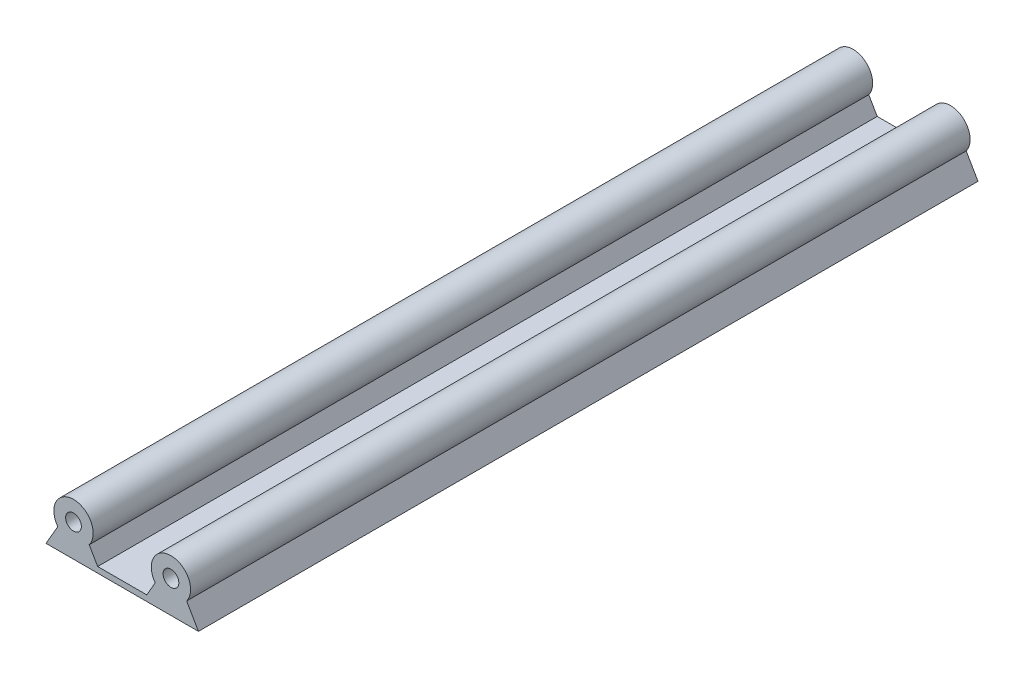
SolidWorks part; units mm, degrees
ref_plane "Front Plane" through (0, 0, 0) normal (0, 0, 1) x (1, 0, 0)
ref_plane "Top Plane" through (0, 0, 0) normal (0, 1, 0) x (1, 0, 0)
ref_plane "Right Plane" through (0, 0, 0) normal (1, 0, 0) x (0, 0, -1)
sketch "Sketch1" plane through (0, 0, 0) normal (0, 0, 1) x (1, 0, 0)
  line L0 (-4, -3) -> (4, -3) construction
  line L1 (-4, -3) -> (-7, -8.1962)
  line L2 (4, -3) -> (7, -8.1962)
  line L3 (-7, -8.1962) -> (7, -8.1962)
  line L4 (28.8, -3) -> (31.8, -8.1962)
  line L5 (17.8, -8.1962) -> (31.8, -8.1962)
  line L6 (20.8, -3) -> (17.8, -8.1962)
  circle A0 centre (0, 0) radius 5
  arc A1 (-4, -3) -> (4, -3) centre (0, 0) cw
  arc A2 (20.8, -3) -> (28.8, -3) centre (24.8, 0) cw
  dimension "D1" = 3
  dimension "D2" = 2
  dimension "D3" = 8
extrude "Boss-Extrude1" add sketch "Sketch1" along normal blind 220 contours A0 L0 | L0 A0 | A0 L1 L3 L2 | L4 L5 L6 A2
sketch "Sketch3" plane through (0, 0, 220) normal (0, 0, 1) x (1, 0, 0)
  line L0 (7, -8.1962) -> (17.8, -8.1962)
  line L1 (6.15, -6.7239) -> (18.65, -6.7239)
  line L2 (4, -3) -> (7, -8.1962) construction
  line L3 (20.8, -3) -> (17.8, -8.1962) construction
  line L4 (18.65, -6.7239) -> (18.65, -8.1962)
  line L5 (17.8, -8.1962) -> (31.8, -8.1962) construction
  line L6 (18.65, -8.1962) -> (17.8, -8.1962)
  line L7 (6.15, -6.7239) -> (6.15, -8.1962)
  line L8 (-7, -8.1962) -> (7, -8.1962) construction
  line L9 (6.15, -8.1962) -> (7, -8.1962)
  dimension "D1" = 12.5
sketch "Sketch4" plane through (0, -8.1962, 0) normal (0, -1, 0) x (1, 0, 0)
  line L0 (24.8, 220) -> (24.8, 0) construction
  line L1 (17.8, 220) -> (31.8, 220) construction
  line L2 (17.8, 0) -> (31.8, 0) construction
  line L3 (0, 0) -> (0, 220) construction
  line L4 (-7, 220) -> (7, 220) construction
  circle A0 centre (0, 198.2) radius 3.2
  circle A1 centre (24.8, 198.2) radius 3.2
  circle A2 centre (24.8, 173.2) radius 3.2
  circle A3 centre (24.8, 148.2) radius 3.2
  circle A4 centre (24.8, 123.2) radius 3.2
  circle A5 centre (24.8, 98.2) radius 3.2
  circle A6 centre (24.8, 73.2) radius 3.2
  circle A7 centre (24.8, 48.2) radius 3.2
  circle A8 centre (24.8, 23.2) radius 3.2
  circle A9 centre (0, 173.2) radius 3.2
  circle A10 centre (0, 148.2) radius 3.2
  circle A11 centre (0, 123.2) radius 3.2
  circle A12 centre (0, 98.2) radius 3.2
  circle A13 centre (0, 73.2) radius 3.2
  circle A14 centre (0, 48.2) radius 3.2
  circle A15 centre (0, 23.2) radius 3.2
  dimension "D1" = 2
  dimension "D4" = 6.4
  dimension "D3" = 23.2
  dimension "D2" = 8
extrude "Boss-Extrude4" add sketch "Sketch3" against normal blind 220
sketch "Sketch5" plane through (0, 0, 0) normal (0, 0, -1) x (-1, 0, 0)
  circle A0 centre (0, 0) radius 1.37
  circle A1 centre (-24.8, 0) radius 1.37
  dimension "D1" = 2
extrude "Cut-Extrude1" cut sketch "Sketch5" against normal blind 7
sketch "Sketch6" plane through (0, 0, 220) normal (0, 0, 1) x (1, 0, 0)
  circle A0 centre (0, 0) radius 1.37
  circle A1 centre (24.8, 0) radius 1.37
  dimension "D1" = 2
extrude "Cut-Extrude2" cut sketch "Sketch6" against normal blind 7
sketch "Sketch9" plane through (0, 0, 0) normal (0, 0, -1) x (-1, 0, 0)
  line L6 (-28.8, -3) -> (-31.8, -8.1962)
  line L7 (-31.8, -8.1962) -> (7, -8.1962)
  line L8 (7, -8.1962) -> (4, -3)
  line L9 (-4, -3) -> (-6.15, -6.7239)
  line L10 (-6.15, -6.7239) -> (-18.65, -6.7239)
  line L11 (-18.65, -6.7239) -> (-20.8, -3)
  line L12 (-28.8, -3) -> (-31.8, -8.1962)
  line L13 (-31.8, -8.1962) -> (7, -8.1962)
  line L14 (7, -8.1962) -> (4, -3)
  line L15 (-4, -3) -> (-6.15, -6.7239)
  line L16 (-6.15, -6.7239) -> (-18.65, -6.7239)
  line L17 (-18.65, -6.7239) -> (-20.8, -3)
  arc A2 (4, -3) -> (-4, -3) centre (0, 0) ccw
  arc A3 (-20.8, -3) -> (-28.8, -3) centre (-24.8, 0) ccw
  arc A4 (4, -3) -> (-4, -3) centre (0, 0) ccw
  arc A5 (-20.8, -3) -> (-28.8, -3) centre (-24.8, 0) ccw
  dimension "D1" = 0
extrude "Cut-Extrude4" cut sketch "Sketch9" against normal blind 10.8
sketch "Sketch10" plane through (0, 0, 220) normal (0, 0, 1) x (1, 0, 0)
  line L6 (20.8, -3) -> (18.65, -6.7239)
  line L7 (18.65, -6.7239) -> (6.15, -6.7239)
  line L8 (6.15, -6.7239) -> (4, -3)
  line L9 (-4, -3) -> (-7, -8.1962)
  line L10 (-7, -8.1962) -> (31.8, -8.1962)
  line L11 (31.8, -8.1962) -> (28.8, -3)
  line L12 (20.8, -3) -> (18.65, -6.7239)
  line L13 (18.65, -6.7239) -> (6.15, -6.7239)
  line L14 (6.15, -6.7239) -> (4, -3)
  line L15 (-4, -3) -> (-7, -8.1962)
  line L16 (-7, -8.1962) -> (31.8, -8.1962)
  line L17 (31.8, -8.1962) -> (28.8, -3)
  arc A2 (4, -3) -> (-4, -3) centre (0, 0) ccw
  arc A3 (28.8, -3) -> (20.8, -3) centre (24.8, 0) ccw
  arc A4 (4, -3) -> (-4, -3) centre (0, 0) ccw
  arc A5 (28.8, -3) -> (20.8, -3) centre (24.8, 0) ccw
  dimension "D1" = 0
extrude "Cut-Extrude5" cut sketch "Sketch10" against normal blind 10.8
sketch "Sketch11" plane through (0, 0, 209.2) normal (0, 0, 1) x (1, 0, 0)
  circle A0 centre (0, 0) radius 2
  circle A1 centre (24.8, 0) radius 2
  dimension "D1" = 2
extrude "Cut-Extrude6" cut sketch "Sketch11" against normal blind 7
sketch "Sketch12" plane through (0, 0, 10.8) normal (0, 0, -1) x (-1, 0, 0)
  circle A0 centre (0, 0) radius 1.5
  circle A1 centre (-24.8, 0) radius 1.5
  dimension "D1" = 2
  dimension "D2" = 3
extrude "Cut-Extrude7" cut sketch "Sketch12" against normal blind 7
sketch "Sketch13" plane through (0, 0, 209.2) normal (0, 0, 1) x (1, 0, 0)
  line L0 (-7, -8.1962) -> (31.8, -8.1962) construction
  line L1 (-12.6, 41.8038) -> (37.4, 41.8038)
  line L2 (-12.6, 41.8038) -> (-12.6, -8.1962)
  line L3 (-12.6, -8.1962) -> (37.4, -8.1962)
  line L4 (37.4, 41.8038) -> (37.4, -8.1962)
  point P8 (12.4, -8.1962)
  point P9 (12.4, -8.1962)
  dimension "D1" = 50
  dimension "D2" = 50
extrude "Boss-Extrude5" [suppressed] add sketch "Sketch13" against normal blind 10
sketch "Sketch14" [suppressed] plane through (0, 0, 199.2) normal (0, 0, -1) x (-1, 0, 0)
  line L0 (-12.4, -8.1962) -> (-12.4, 41.8038) construction
  line L1 (-31.8, -8.1962) -> (7, -8.1962) construction
  line L2 (-37.4, 41.8038) -> (12.6, 41.8038) construction
  circle A0 centre (-12.4, 22.3038) radius 5
  dimension "D2" = 10
  dimension "D1" = 30.5
extrude "Cut-Extrude8" [suppressed] cut sketch "Sketch14" against normal blind 5
extrude "Cut-Extrude9" cut sketch "Sketch4" against normal blind 5 contours A15 | A8 | A0 | A1
